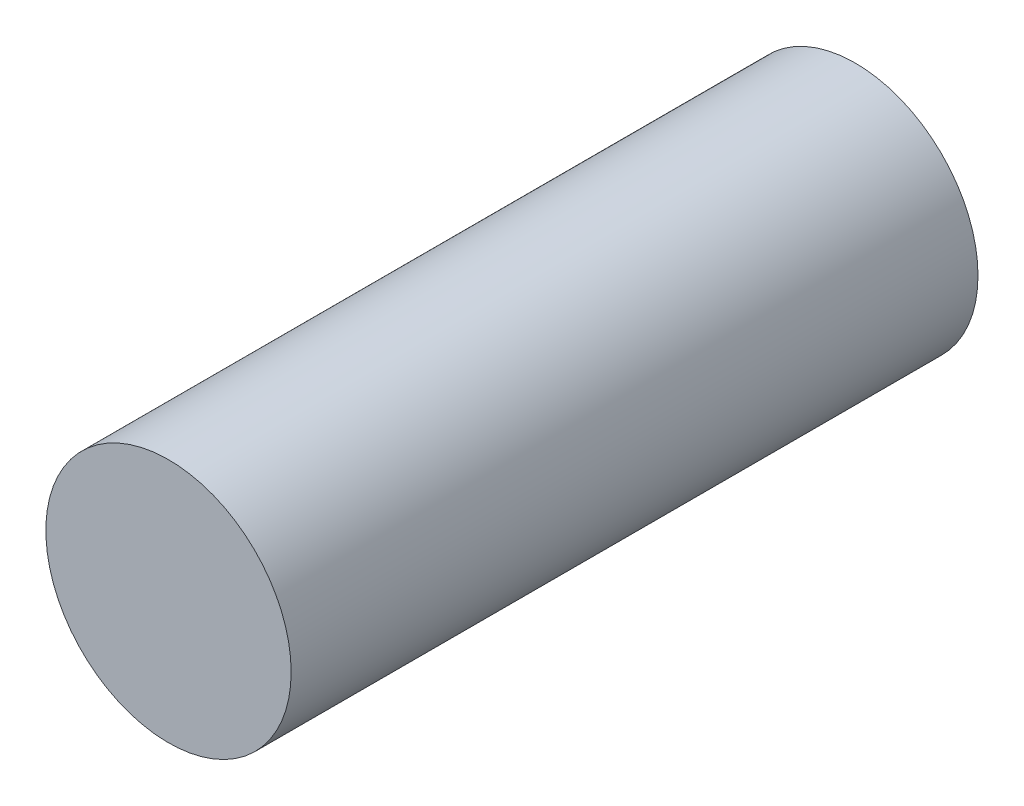
SolidWorks part; units mm, degrees
ref_plane "Front Plane" through (0, 0, 0) normal (0, 0, 1) x (1, 0, 0)
ref_plane "Top Plane" through (0, 0, 0) normal (0, 1, 0) x (1, 0, 0)
ref_plane "Right Plane" through (0, 0, 0) normal (1, 0, 0) x (0, 0, -1)
sketch "Sketch1" plane through (0, 0, 0) normal (0, 0, 1) x (1, 0, 0)
  circle A0 centre (0, 0) radius 12.5
  dimension "D1" = 25
extrude "Boss-Extrude1" add sketch "Sketch1" along normal blind 70
